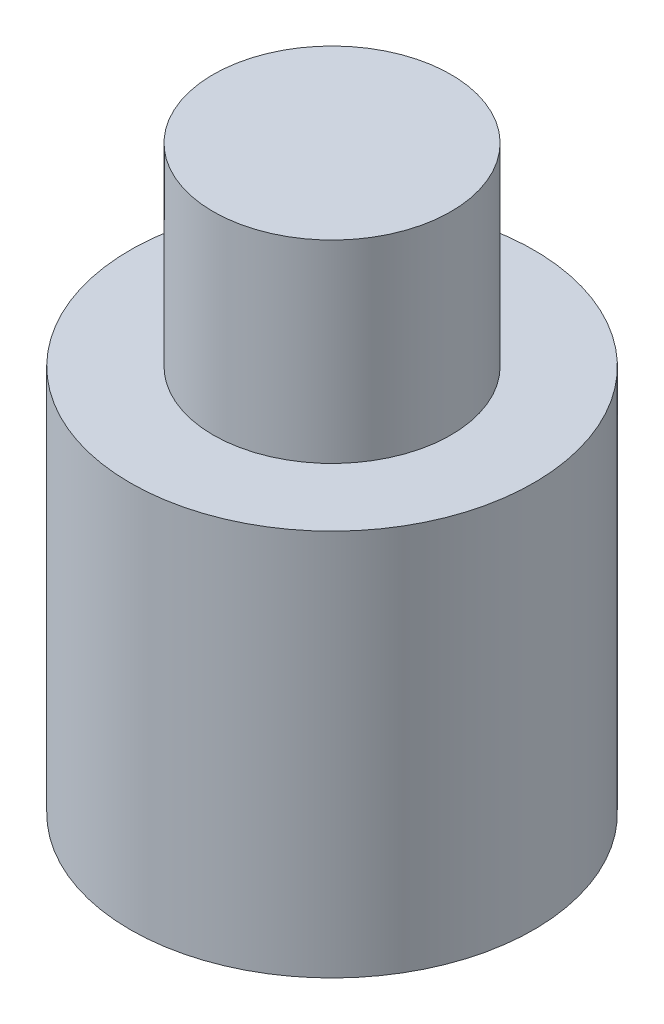
SolidWorks part; units mm, degrees
ref_plane "Alzado" through (0, 0, 0) normal (0, 0, 1) x (1, 0, 0)
ref_plane "Planta" through (0, 0, 0) normal (0, 1, 0) x (1, 0, 0)
ref_plane "Vista lateral" through (0, 0, 0) normal (1, 0, 0) x (0, 0, -1)
sketch "Croquis1" plane through (0, 0, 0) normal (0, 1, 0) x (1, 0, 0)
  circle A0 centre (0, 0) radius 2.65
  circle A1 centre (0, 0) radius 3.65
  dimension "D1" = 5.3
  dimension "D2" = 1
extrude "Saliente-Extruir1" add sketch "Croquis1" along normal blind 3.5
sketch "Croquis2" plane through (0, 3.5, 0) normal (0, 1, 0) x (1, 0, 0)
  circle A0 centre (0, 0) radius 3.65
extrude "Saliente-Extruir2" add sketch "Croquis2" along normal blind 3.5
sketch "Croquis3" plane through (0, 7, 0) normal (0, 1, 0) x (1, 0, 0)
  circle A0 centre (0, 0) radius 2.15
  dimension "D1" = 4.3
extrude "Saliente-Extruir3" add sketch "Croquis3" along normal blind 3.5
